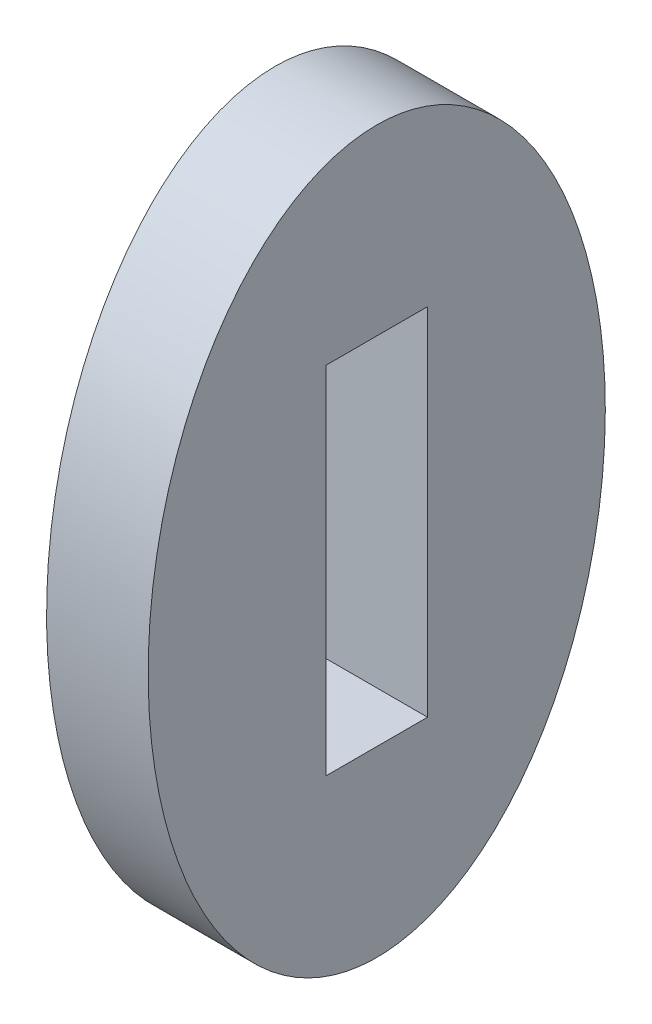
SolidWorks part; units mm, degrees
ref_plane "Front Plane" through (0, 0, 0) normal (0, 0, 1) x (1, 0, 0)
ref_plane "Top Plane" through (0, 0, 0) normal (0, 1, 0) x (1, 0, 0)
ref_plane "Right Plane" through (0, 0, 0) normal (1, 0, 0) x (0, 0, -1)
sketch "Sketch1" plane through (0, 0, 0) normal (1, 0, 0) x (0, 0, -1)
  line L1 (-3.175, -11.1125) -> (3.175, -11.1125)
  line L2 (-3.175, -11.1125) -> (-3.175, 11.1125)
  line L3 (-3.175, 11.1125) -> (3.175, 11.1125)
  line L4 (3.175, -11.1125) -> (3.175, 11.1125)
  line L5 (-3.175, -11.1125) -> (3.175, 11.1125) construction
  line L6 (-3.175, 11.1125) -> (3.175, -11.1125) construction
  ellipse E0 centre (0, 0) end of major axis (0, 22.5365) minor radius 14.2875
  point P8 (0, 22.5365)
  point P12 (0, 0)
  point P13 (-14.2875, 0)
  dimension "D1" = 6.35
  dimension "D2" = 22.225
  dimension "D3" = 28.575
extrude "Boss-Extrude1" add sketch "Sketch1" along normal blind 6.35
